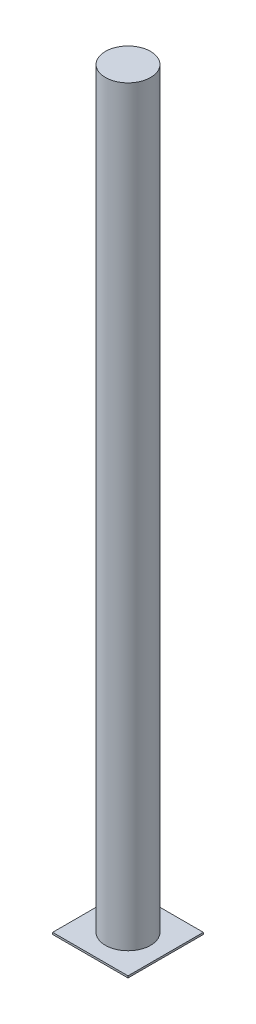
SolidWorks part; units mm, degrees
ref_plane "前基準面" through (0, 0, 0) normal (0, 0, 1) x (1, 0, 0)
ref_plane "上基準面" through (0, 0, 0) normal (0, 1, 0) x (1, 0, 0)
ref_plane "右基準面" through (0, 0, 0) normal (1, 0, 0) x (0, 0, -1)
sketch "草圖1" plane through (0, 0, 0) normal (0, 1, 0) x (1, 0, 0)
  circle A0 centre (0, 0) radius 60
  dimension "D1" = 120
extrude "填料-伸長1" add sketch "草圖1" along normal blind 2000
sketch "草圖2" plane through (0, 0, 0) normal (0, -1, 0) x (1, 0, 0)
  line L1 (-100, 100) -> (100, 100)
  line L2 (-100, 100) -> (-100, -100)
  line L3 (-100, -100) -> (100, -100)
  line L4 (100, 100) -> (100, -100)
  line L5 (-100, 100) -> (100, -100) construction
  line L6 (-100, -100) -> (100, 100) construction
  point P0 (0, 0)
  dimension "D1" = 200
  dimension "D2" = 200
extrude "填料-伸長2" add sketch "草圖2" against normal blind 5
